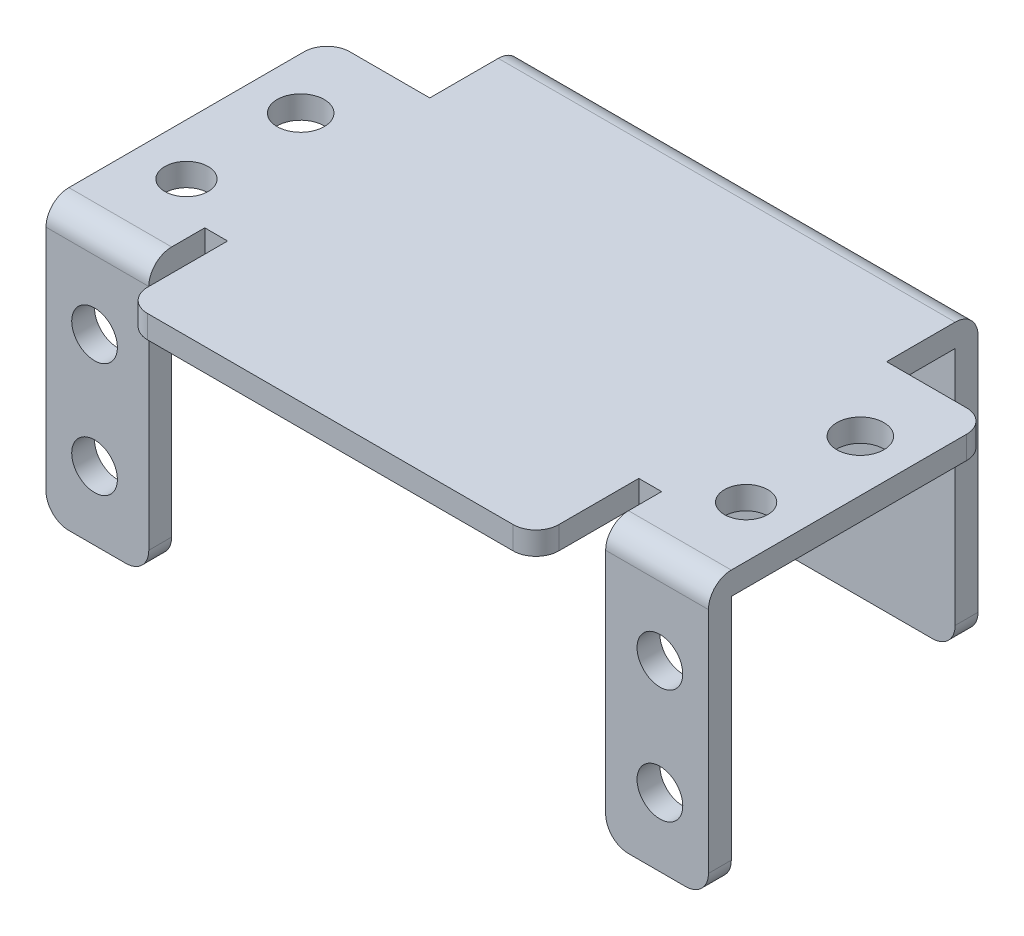
SolidWorks part; units mm, degrees
ref_plane "前视基准面" through (0, 0, 0) normal (0, 0, 1) x (1, 0, 0)
ref_plane "上视基准面" through (0, 0, 0) normal (0, 1, 0) x (1, 0, 0)
ref_plane "右视基准面" through (0, 0, 0) normal (1, 0, 0) x (0, 0, -1)
other "Configuration Table"
ref_plane "基准面1" through (29, 0, 0) normal (1, 0, 0) x (0, 0, -1)
sketch "草图1" plane through (29, 0, 0) normal (1, 0, 0) x (0, 0, -1)
  line L0 (-32.6, 1) -> (0, 1)
  line L1 (0, 1) -> (0, 25)
  line L2 (0, 25) -> (-32.6, 25)
  line L3 (-32.6, 25) -> (-32.6, 1)
extrude "凸台-拉伸1" add sketch "草图1" against normal blind 9
sketch "草图2" plane through (20, 0, 0) normal (-1, 0, 0) x (0, 0, 1)
  line L0 (30.6, 23) -> (0, 23)
  line L1 (0, 23) -> (0, 1)
  line L2 (0, 1) -> (30.6, 1)
  line L3 (30.6, 1) -> (30.6, 23)
extrude "切除-拉伸1" cut sketch "草图2" against normal through all
sketch "草图3" plane through (20, 0, 0) normal (-1, 0, 0) x (0, 0, 1)
  line L0 (27.7, 23) -> (0, 23)
  line L1 (0, 23) -> (0, 25)
  line L2 (0, 25) -> (27.7, 25)
  line L3 (27.7, 25) -> (27.7, 23)
extrude "凸台-拉伸2" add sketch "草图3" along normal blind 49
sketch "草图4" plane through (0, 0, 27.7) normal (0, 0, 1) x (1, 0, 0)
  line L0 (-29, 23) -> (-29, 25)
  line L1 (-29, 25) -> (-20, 25)
  line L2 (-20, 25) -> (-20, 23)
  line L3 (-20, 23) -> (-29, 23)
extrude "凸台-拉伸3" add sketch "草图4" along normal blind 4.9
sketch "草图5" plane through (0, 23, 0) normal (0, -1, 0) x (1, 0, 0)
  line L0 (-20, 30.6) -> (-29, 30.6)
  line L1 (-29, 30.6) -> (-29, 32.6)
  line L2 (-29, 32.6) -> (-20, 32.6)
  line L3 (-20, 32.6) -> (-20, 30.6)
extrude "凸台-拉伸4" add sketch "草图5" along normal blind 22
sketch "草图6" plane through (0, 25, 0) normal (0, 1, 0) x (-1, 0, 0)
  line L0 (29, 8) -> (20, 8)
  line L1 (20, 8) -> (20, 0)
  line L2 (20, 0) -> (29, 0)
  line L3 (29, 0) -> (29, 8)
extrude "切除-拉伸2" cut sketch "草图6" against normal through all
sketch "草图7" plane through (0, 25, 0) normal (0, 1, 0) x (-1, 0, 0)
  line L0 (-20, 0) -> (-20, 8)
  line L1 (-20, 8) -> (-29, 8)
  line L2 (-29, 8) -> (-29, 0)
  line L3 (-29, 0) -> (-20, 0)
extrude "切除-拉伸3" cut sketch "草图7" against normal through all
sketch "草图8" plane through (0, 23, 0) normal (0, -1, 0) x (1, 0, 0)
  line L0 (-20, 2) -> (20, 2)
  line L1 (20, 2) -> (20, 0)
  line L2 (20, 0) -> (-20, 0)
  line L3 (-20, 0) -> (-20, 2)
extrude "凸台-拉伸5" add sketch "草图8" along normal blind 23
sketch "草图9" plane through (0, 0, 27.7) normal (0, 0, 1) x (1, 0, 0)
  line L0 (-18, 25) -> (18, 25)
  line L1 (18, 25) -> (18, 23)
  line L2 (18, 23) -> (-18, 23)
  line L3 (-18, 23) -> (-18, 25)
extrude "凸台-拉伸6" add sketch "草图9" along normal blind 9
hole_wizard "Ø4.0 (4) 直径孔1" positions "草图11" profile "草图10" hole size "Ø4.0" standard "ANSI Metric" end condition through all
sketch "草图11" plane through (0, 0, 30.6) normal (0, 0, -1) x (-1, 0, 0)
  point P0 (-24.75, 17)
  point P1 (-24.75, 7)
  point P2 (24.75, 17)
  point P3 (24.75, 7)
sketch "草图10" plane through (24.75, 17, 30.6) normal (1, 0, 0) x (0, 1, 0)
  line L0 (0, 0) -> (0, 6.1)
  line L1 (0, 6.1) -> (2, 6.1)
  line L2 (2, 6.1) -> (2, 0)
  line L5 (2, 0) -> (0, 0)
  line L11 (0, -6.35) -> (0, 107.95) construction
  dimension "通孔孔直径" = 4
  dimension "通孔孔深度" = 6.1
fillet "圆角1" radius 2 13 edges at (0, 25, 0) (-18, 24, 36.7) (29, 24, 8) (24.5, 25, 32.6) (29, 1, 31.6) (20, 1, 31.6) (20, 0, 1) (-20, 1, 31.6) (18, 24, 36.7) (-29, 1, 31.6) (-29, 24, 8) (-24.5, 25, 32.6) (-20, 0, 1)
sketch "草图12" plane through (0, 23, 0) normal (0, -1, 0) x (1, 0, 0)
  line L0 (-24.5, 24.8) -> (-24.5, 14.8)
  line L1 (-24.5, 14.8) -> (-24.5, 8)
  line L2 (-27, 8) -> (-20, 8) construction
  line L3 (0, 0) -> (0, 46.3661) construction
  line L5 (24.5, 14.8) -> (24.5, 8)
  line L6 (24.5, 24.8) -> (24.5, 14.8)
  circle A0 centre (-24.5, 24.8) radius 1.8977
  circle A1 centre (-24.5, 14.8) radius 2.0621
  circle A2 centre (24.5, 14.8) radius 2.0621
  circle A3 centre (24.5, 24.8) radius 1.8977
  dimension "D1" = 10
  dimension "D2" = 6.8
extrude "切除-拉伸4" cut sketch "草图12" against normal through all
sketch "草图15" plane through (0, 0, 32.6) normal (0, 0, 1) x (1, 0, 0)
  line L0 (0, 25) -> (0, 0) construction
  line L1 (16, 25) -> (-16, 25) construction
